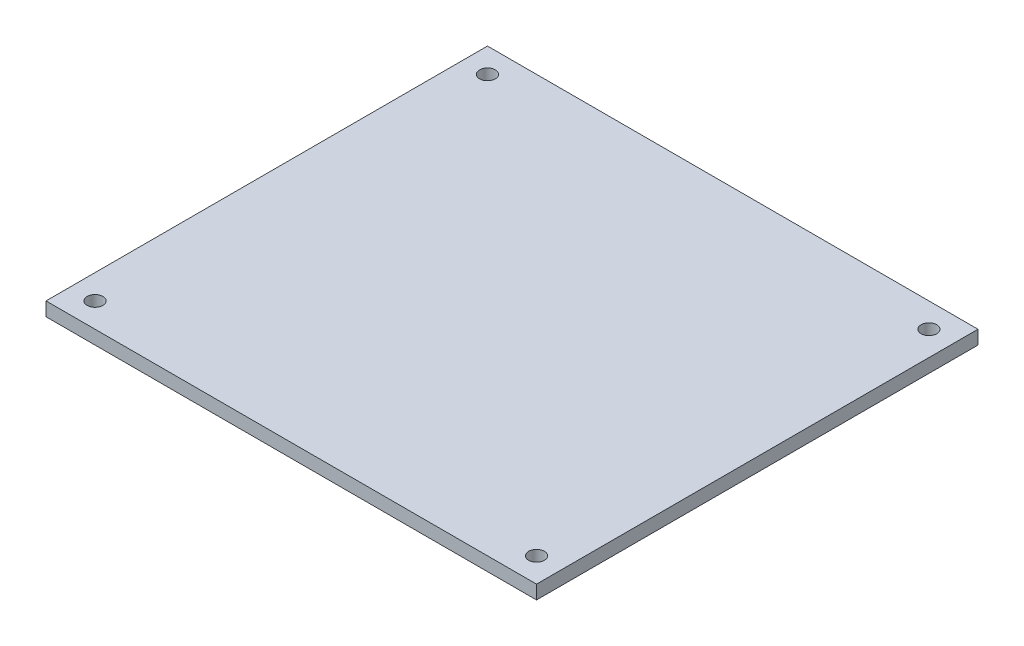
SolidWorks part; units mm, degrees
ref_plane "前视基准面" through (0, 0, 0) normal (0, 0, 1) x (1, 0, 0)
ref_plane "上视基准面" through (0, 0, 0) normal (0, 1, 0) x (1, 0, 0)
ref_plane "右视基准面" through (0, 0, 0) normal (1, 0, 0) x (0, 0, -1)
sketch "草图1" plane through (0, 0, 0) normal (0, 1, 0) x (1, 0, 0)
  line L0 (50, 90) -> (50, -26.9383) construction
  line L1 (0, 0) -> (100, 0)
  line L2 (0, 0) -> (0, 90)
  line L3 (0, 90) -> (100, 90)
  line L4 (100, 0) -> (100, 90)
  line L5 (-18.5078, 45) -> (123.301, 45) construction
  circle A0 centre (5, 85) radius 1.6
  circle A1 centre (95, 85) radius 1.6
  circle A2 centre (95, 5) radius 1.6
  circle A3 centre (5, 5) radius 1.6
  dimension "D3" = 5
  dimension "D4" = 5
  dimension "D1" = 90
  dimension "D2" = 100
extrude "凸台-拉伸1" add sketch "草图1" along normal blind 2.8
